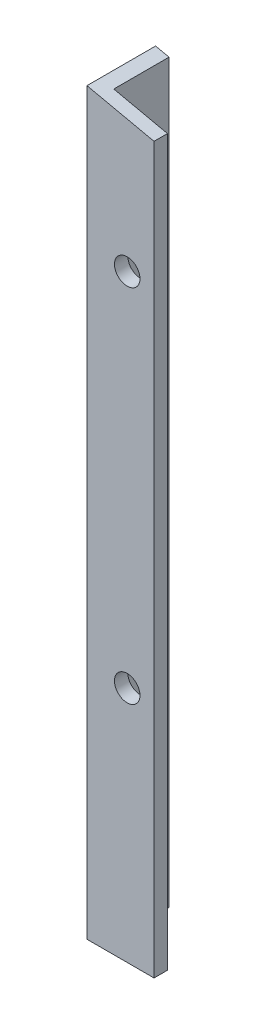
SolidWorks part; units mm, degrees
ref_plane "Front Plane" through (0, 0, 0) normal (0, 0, 1) x (1, 0, 0)
ref_plane "Top Plane" through (0, 0, 0) normal (0, 1, 0) x (1, 0, 0)
ref_plane "Right Plane" through (0, 0, 0) normal (1, 0, 0) x (0, 0, -1)
sketch "Sketch1" plane through (0, 0, 0) normal (0, 1, 0) x (1, 0, 0)
  line L0 (0, 0) -> (0, 12.9997)
  line L1 (0, 0) -> (12.7, 0)
  line L2 (0, 12.9997) -> (2.54, 12.9997)
  line L3 (2.54, 12.9997) -> (2.54, 2.54)
  line L4 (2.54, 2.54) -> (12.7, 2.54)
  line L5 (12.7, 2.54) -> (12.7, 0)
  dimension "D1" = 12.9997
  dimension "D2" = 12.7
  dimension "D3" = 2.54
  dimension "D4" = 2.54
extrude "Boss-Extrude1" add sketch "Sketch1" along normal blind 140
sketch "Sketch2" plane through (0, 0, -2.54) normal (0, 0, -1) x (-1, 0, 0)
  line L0 (0, 132.9718) -> (0, 140)
  line L1 (0, 140) -> (0, 0) construction
  line L2 (0, 140) -> (-16.3773, 136.4142)
  line L3 (-16.3773, 136.4142) -> (-11.1597, 144.6347)
  line L4 (-11.1597, 144.6347) -> (0, 140)
  line M6 (-2.54, 0) -> (-2.54, 140)
  line M7 (-2.54, 140) -> (-12.7, 140)
  line M8 (-12.7, 140) -> (-12.7, 0)
  dimension "D1" = 77.65
extrude "Cut-Extrude1" cut sketch "Sketch2" against normal blind 6.35 and the other way blind 18.35 contours L4 L3 L2 M8 M7 M6 | L2 M6 M7 M8
sketch "Sketch3" plane through (0, 0, -2.54) normal (0, 0, -1) x (-1, 0, 0)
  line L1 (-2.54, 139.4439) -> (-12.7, 137.2193) construction
  circle A0 centre (-7.62, 113.3316) radius 2.415
  point P4 (-7.62, 138.3316)
  dimension "D2" = 4.83
  dimension "D1" = 25
extrude "Cut-Extrude2" cut sketch "Sketch3" against normal blind 10
sketch "Sketch4" plane through (2.54, 0, 0) normal (1, 0, 0) x (0, 0, -1)
  circle A1 centre (7.7699, 94.4439) radius 2.415
  dimension "D3" = 4.83
extrude "Cut-Extrude3" cut sketch "Sketch4" against normal blind 10
sketch "Sketch5" plane through (2.54, 0, 0) normal (1, 0, 0) x (0, 0, -1)
  circle A0 centre (7.7699, 60) radius 2.415
  dimension "D3" = 4.83
extrude "Cut-Extrude4" cut sketch "Sketch5" against normal blind 10
sketch "Sketch6" plane through (0, 0, -2.54) normal (0, 0, -1) x (-1, 0, 0)
  line L0 (-12.7, 0) -> (-2.54, 0) construction
  circle A0 centre (-7.62, 45) radius 2.415
  dimension "D2" = 4.83
  dimension "D1" = 45
extrude "Cut-Extrude5" cut sketch "Sketch6" against normal blind 10
